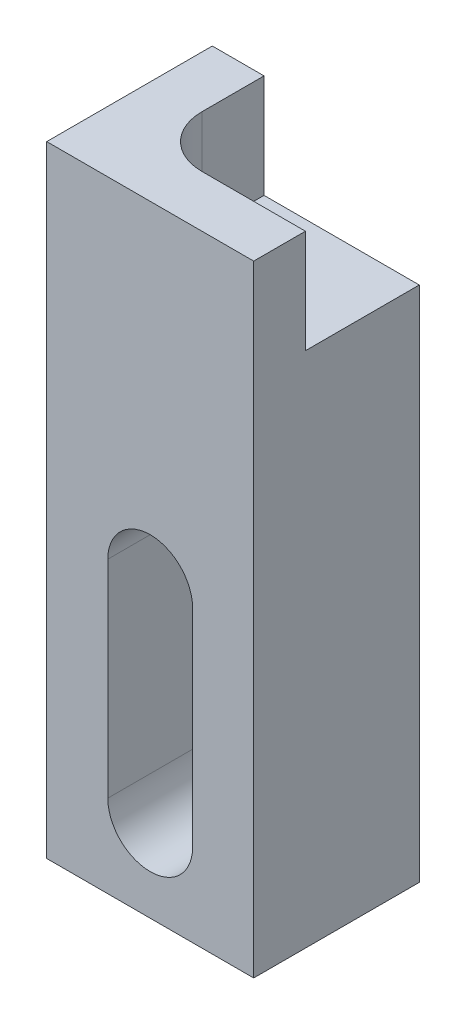
SolidWorks part; units mm, degrees
ref_plane "Front Plane" through (0, 0, 0) normal (0, 0, 1) x (1, 0, 0)
ref_plane "Top Plane" through (0, 0, 0) normal (0, 1, 0) x (1, 0, 0)
ref_plane "Right Plane" through (0, 0, 0) normal (1, 0, 0) x (0, 0, -1)
sketch "Sketch1" plane through (0, 0, 0) normal (0, 0, 1) x (1, 0, 0)
  line L0 (0, -454.7073) -> (0, 22280.66) construction
  line L1 (-454.7073, 0) -> (22280.66, 0) construction
  line L2 (0, 28) -> (0, 8) construction
  line L3 (-10, 0) -> (10, 0)
  line L4 (-10, 0) -> (-10, 60)
  line L5 (-10, 60) -> (10, 60)
  line L6 (10, 0) -> (10, 60)
  line L7 (4.1, 28) -> (4.1, 8)
  line L8 (-4.1, 28) -> (-4.1, 8)
  arc A0 (4.1, 28) -> (-4.1, 28) centre (0, 28) ccw
  arc A1 (-4.1, 8) -> (4.1, 8) centre (0, 8) ccw
  point P9 (0, 60)
  point P12 (0, 18)
  point P17 (-4.1, 18)
  dimension "D1" = 20
  dimension "D2" = 60
  dimension "D3" = 8.2
  dimension "D4" = 20
  dimension "D5" = 8
extrude "Boss-Extrude1" add sketch "Sketch1" along normal mid plane 16
sketch "Sketch2" plane through (0, 60, 0) normal (0, 1, 0) x (1, 0, 0)
  line L0 (0, -1000) -> (0, 49000) construction
  line L1 (-1000, 0) -> (49000, 0) construction
  line L8 (10, -3) -> (0, -3)
  line L10 (10, -8) -> (10, 8) construction
  line L12 (-5, 2) -> (-5, 8)
  line L13 (10, 8) -> (-10, 8) construction
  line L14 (-5, 8) -> (10, 8)
  line L15 (10, 8) -> (10, -3)
  line L16 (-5, -3) -> (-10, -3) construction
  line L17 (-10, -8) -> (-10, 8) construction
  line L18 (-5, -3) -> (-5, -8) construction
  line L19 (10, -8) -> (-10, -8) construction
  arc A1 (0, -3) -> (-5, 2) centre (0, 2) cw
  dimension "D1" = 5
  dimension "D2" = 5
extrude "Cut-Extrude1" cut sketch "Sketch2" against normal blind 10
